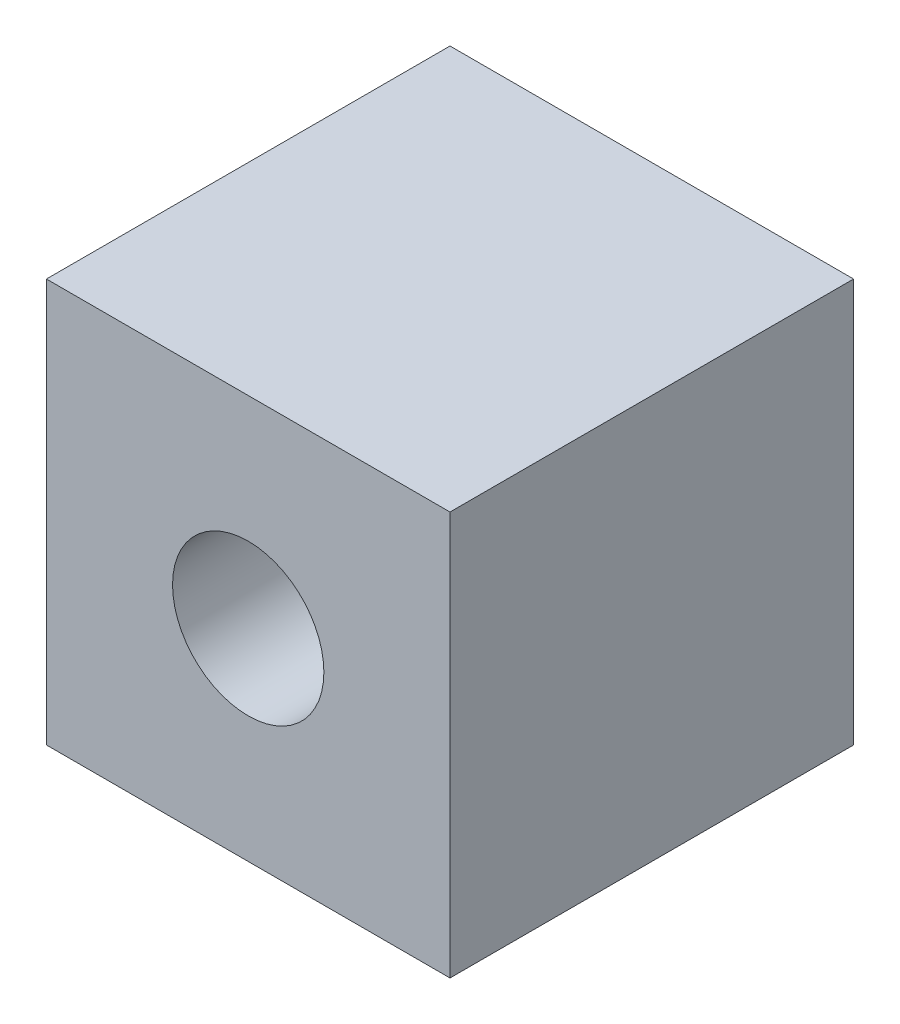
SolidWorks part; units mm, degrees
ref_plane "Front Plane" through (0, 0, 0) normal (0, 0, 1) x (1, 0, 0)
ref_plane "Top Plane" through (0, 0, 0) normal (0, 1, 0) x (1, 0, 0)
ref_plane "Right Plane" through (0, 0, 0) normal (1, 0, 0) x (0, 0, -1)
sketch "Sketch1" plane through (0, 0, 0) normal (0, 0, 1) x (1, 0, 0)
  line L1 (-508.001, -508.001) -> (508.001, -508.001)
  line L2 (-508.001, -508.001) -> (-508.001, 508.001)
  line L3 (-508.001, 508.001) -> (508.001, 508.001)
  line L4 (508.001, -508.001) -> (508.001, 508.001)
  line L5 (-508.001, -508.001) -> (508.001, 508.001) construction
  line L6 (-508.001, 508.001) -> (508.001, -508.001) construction
  point P0 (0, 0)
  dimension "D1" = 1016.002
  dimension "D2" = 1016.002
extrude "Boss-Extrude1" add sketch "Sketch1" along normal mid plane 1016 contours L3 L4 L1 L2
sketch "Sketch2" plane through (0, 0, 508) normal (0, 0, 1) x (1, 0, 0)
  circle A0 centre (0, 0) radius 190.5004
  dimension "D1" = 381.0008
extrude "Cut-Extrude1" cut sketch "Sketch2" against normal through all contours A0
equation "\"Depth\"= 40"
equation "\"D1@Boss-Extrude1\"= \"Depth\""
